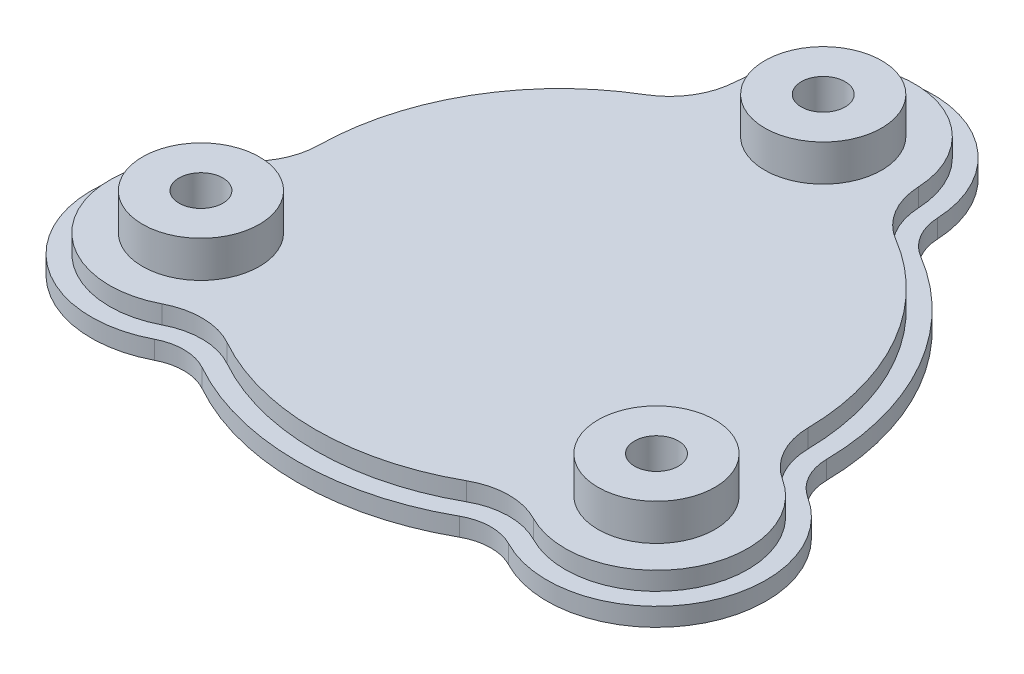
SolidWorks part; units mm, degrees
material "PE Low/Medium Density"
ref_plane "Front Plane" through (0, 0, 0) normal (0, 0, 1) x (1, 0, 0)
ref_plane "Top Plane" through (0, 0, 0) normal (0, 1, 0) x (1, 0, 0)
ref_plane "Right Plane" through (0, 0, 0) normal (1, 0, 0) x (0, 0, -1)
sketch "Sketch1" plane through (0, 0, 0) normal (0, 1, 0) x (1, 0, 0)
  arc A0 (-18.4011, 30.9419) -> (-35.997, 0.4649) centre (0, 0) ccw
  arc A1 (14.9858, 36.6534) -> (-14.9858, 36.6534) centre (0, 36) ccw
  arc A2 (24.2499, -31.3048) -> (39.2357, -5.3487) centre (31.1769, -18) ccw
  arc A3 (-39.2357, -5.3487) -> (-24.2499, -31.3048) centre (-31.1769, -18) ccw
  arc A4 (35.997, 0.4649) -> (18.4011, 30.9419) centre (0, 0) ccw
  arc A5 (-17.5959, -31.4068) -> (17.5959, -31.4068) centre (0, 0) ccw
  arc A6 (39.2357, -5.3487) -> (35.997, 0.4649) centre (42.9964, 0.5553) cw
  arc A7 (24.2499, -31.3048) -> (17.5959, -31.4068) centre (21.0173, -37.5136) ccw
  arc A8 (-24.2499, -31.3048) -> (-17.5959, -31.4068) centre (-21.0173, -37.5136) cw
  arc A9 (-39.2357, -5.3487) -> (-35.997, 0.4649) centre (-42.9964, 0.5553) ccw
  arc A10 (-14.9858, 36.6534) -> (-18.4011, 30.9419) centre (-21.9791, 36.9583) cw
  arc A11 (14.9858, 36.6534) -> (18.4011, 30.9419) centre (21.9791, 36.9583) ccw
  point P6 (-73.0329, -43)
  point P7 (0, 0)
  point P11 (0, 0)
  point P12 (0, 0)
  point P17 (35.806, -3.7322)
  point P22 (-21.1352, -29.1428)
  dimension "D1" = 72
  dimension "D2" = 30
  dimension "D5" = 7
  dimension "D3" = 36
  dimension "D4" = 3
extrude "Boss-Extrude1" add sketch "Sketch1" along normal blind 2.5
sketch "Sketch2" plane through (0, 2.5, 0) normal (0, 1, 0) x (1, 0, 0)
  arc A24 (33.4972, 0.4326) -> (37.8925, -7.4572) centre (42.9964, 0.5553) ccw
  arc A25 (33.4972, 0.4326) -> (17.1233, 28.7931) centre (0, 0) ccw
  arc A26 (12.4881, 36.5445) -> (17.1233, 28.7931) centre (21.9791, 36.9583) ccw
  arc A27 (12.4881, 36.5445) -> (-12.4881, 36.5445) centre (0, 36) ccw
  arc A28 (-17.1233, 28.7931) -> (-12.4881, 36.5445) centre (-21.9791, 36.9583) ccw
  arc A29 (-17.1233, 28.7931) -> (-33.4972, 0.4326) centre (0, 0) ccw
  arc A30 (-37.8925, -7.4572) -> (-33.4972, 0.4326) centre (-42.9964, 0.5553) ccw
  arc A31 (-37.8925, -7.4572) -> (-25.4044, -29.0873) centre (-31.1769, -18) ccw
  arc A32 (-16.3739, -29.2257) -> (-25.4044, -29.0873) centre (-21.0173, -37.5136) ccw
  arc A33 (-16.3739, -29.2257) -> (16.3739, -29.2257) centre (0, 0) ccw
  arc A34 (25.4044, -29.0873) -> (16.3739, -29.2257) centre (21.0173, -37.5136) ccw
  arc A35 (25.4044, -29.0873) -> (37.8925, -7.4572) centre (31.1769, -18) ccw
  arc A36 (33.4972, 0.4326) -> (37.8925, -7.4572) centre (42.9964, 0.5553) ccw
  arc A37 (33.4972, 0.4326) -> (17.1233, 28.7931) centre (0, 0) ccw
  arc A38 (12.4881, 36.5445) -> (17.1233, 28.7931) centre (21.9791, 36.9583) ccw
  arc A39 (12.4881, 36.5445) -> (-12.4881, 36.5445) centre (0, 36) ccw
  arc A40 (-17.1233, 28.7931) -> (-12.4881, 36.5445) centre (-21.9791, 36.9583) ccw
  arc A41 (-17.1233, 28.7931) -> (-33.4972, 0.4326) centre (0, 0) ccw
  arc A42 (-37.8925, -7.4572) -> (-33.4972, 0.4326) centre (-42.9964, 0.5553) ccw
  arc A43 (-37.8925, -7.4572) -> (-25.4044, -29.0873) centre (-31.1769, -18) ccw
  arc A44 (-16.3739, -29.2257) -> (-25.4044, -29.0873) centre (-21.0173, -37.5136) ccw
  arc A45 (-16.3739, -29.2257) -> (16.3739, -29.2257) centre (0, 0) ccw
  arc A46 (25.4044, -29.0873) -> (16.3739, -29.2257) centre (21.0173, -37.5136) ccw
  arc A47 (25.4044, -29.0873) -> (37.8925, -7.4572) centre (31.1769, -18) ccw
  dimension "D1" = 2.5
extrude "Boss-Extrude2" add sketch "Sketch2" along normal blind 2.5
sketch "Sketch3" plane through (0, 5, 0) normal (0, 1, 0) x (1, 0, 0)
  circle A0 centre (0, 36) radius 8
  circle A1 centre (31.1769, -18) radius 8
  circle A2 centre (-31.1769, -18) radius 8
  circle A3 centre (0, 36) radius 3
  circle A4 centre (31.1769, -18) radius 3
  circle A5 centre (-31.1769, -18) radius 3
  dimension "D1" = 16
  dimension "D2" = 6
extrude "Boss-Extrude3" add sketch "Sketch3" along normal blind 5
sketch "Sketch4" plane through (0, 0, 0) normal (0, -1, 0) x (1, 0, 0)
  circle A0 centre (31.1769, 18) radius 5.5
  circle A1 centre (0, -36) radius 5.5
  circle A2 centre (-31.1769, 18) radius 5.5
  dimension "D1" = 11
extrude "Cut-Extrude1" cut sketch "Sketch4" against normal blind 5
equation "\"A\" = 36"
equation "\"B\" = 10"
equation "\"C\"= 2.5"
equation "\"D1@Sketch1\"=\"A\"*2"
equation "\"D3@Sketch1\"=\"A\""
equation "\"D1@Boss-Extrude1\"=\"C\""
equation "\"D1@Boss-Extrude2\"=\"C\""
equation "\"D1@Boss-Extrude3\"=\"B\"-\"C\"*2"
equation "\"D1@Cut-Extrude1\"=\"B\"-\"C\"*2"
equation "\"D1@Sketch2\"= \"C\""
